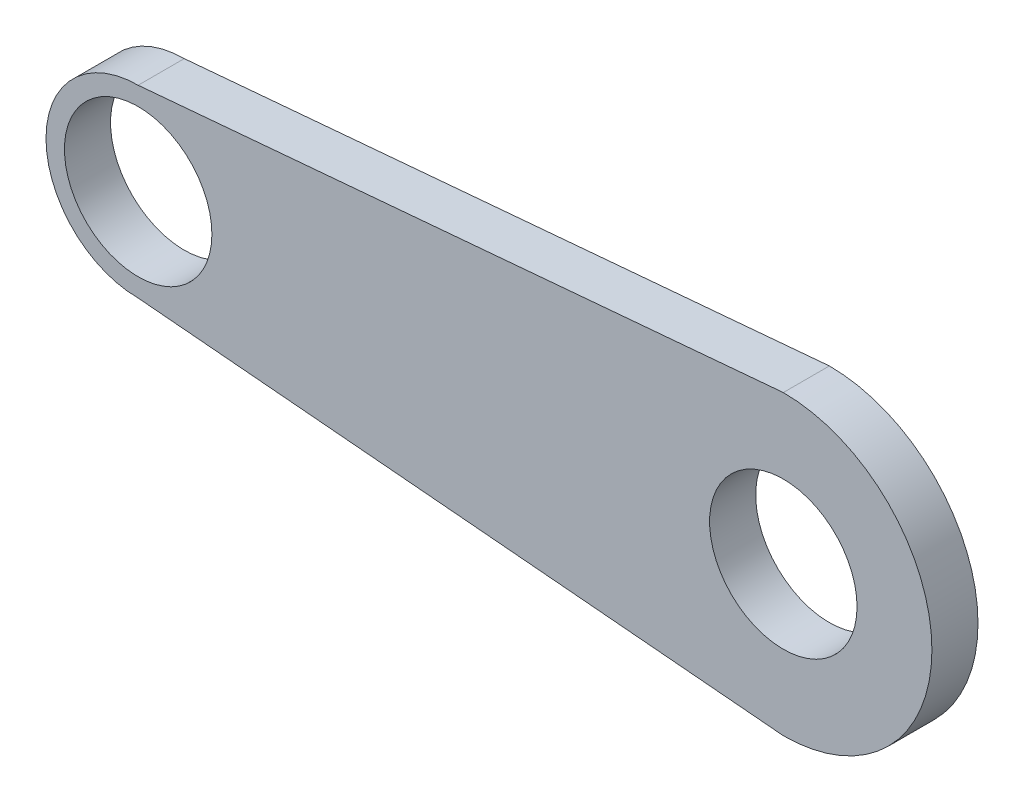
SolidWorks part; units mm, degrees
ref_plane "Front Plane" through (0, 0, 0) normal (0, 0, 1) x (1, 0, 0)
ref_plane "Top Plane" through (0, 0, 0) normal (0, 1, 0) x (1, 0, 0)
ref_plane "Right Plane" through (0, 0, 0) normal (1, 0, 0) x (0, 0, -1)
sketch "Sketch1" plane through (0, 0, 0) normal (0, 0, 1) x (1, 0, 0)
  line L0 (-133.2789, -7.0608) -> (44.5211, 8.4947)
  line L2 (-133.2789, -57.8608) -> (44.5211, -73.4163)
  arc A0 (37.4093, -72.7941) -> (37.4093, 7.8725) centre (44.5211, -32.4608) ccw
  arc A1 (-133.2789, -7.0608) -> (-133.2789, -57.8608) centre (-133.2789, -32.4608) ccw
  circle A2 centre (-133.2789, -32.4608) radius 20.32
  circle A3 centre (44.5211, -32.4608) radius 20.32
  dimension "D2" = 40.64
  dimension "D1" = 25.4
  dimension "D3" = 177.8
extrude "Boss-Extrude1" add sketch "Sketch1" along normal blind 12.7 contours L0 A1 L2 A0 A3 A2
